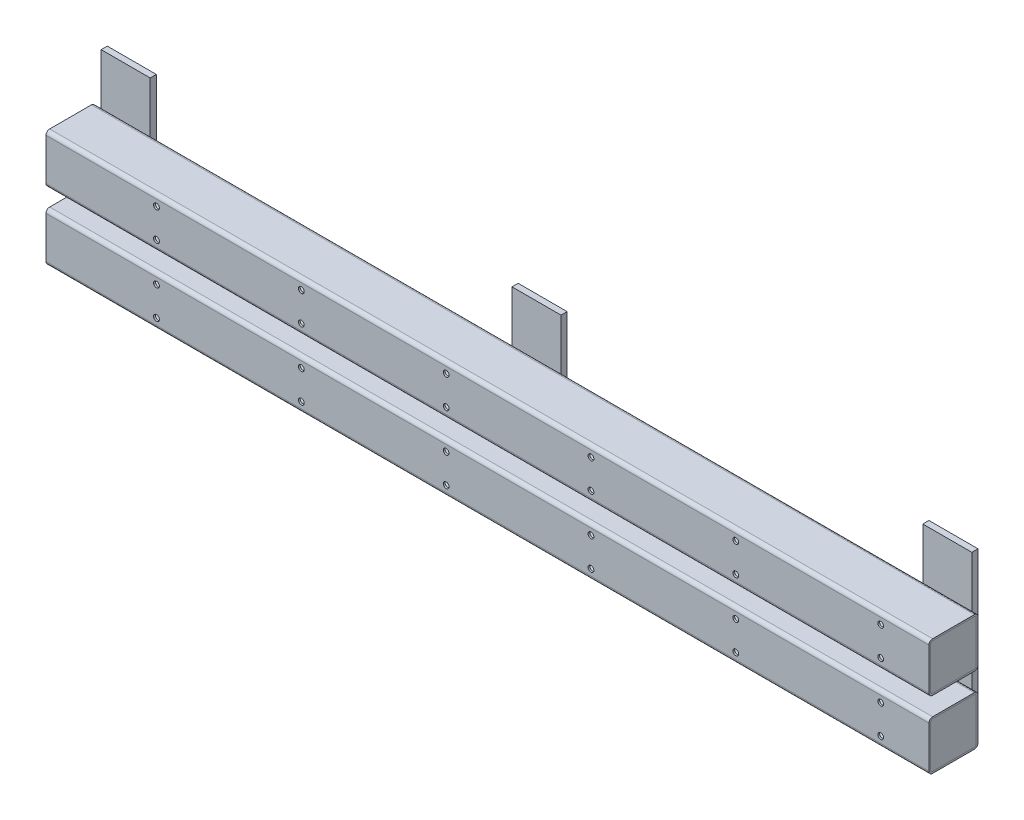
SolidWorks part; units mm, degrees
ref_plane "Front Plane" through (0, 0, 0) normal (0, 0, 1) x (1, 0, 0)
ref_plane "Top Plane" through (0, 0, 0) normal (0, 1, 0) x (1, 0, 0)
ref_plane "Right Plane" through (0, 0, 0) normal (1, 0, 0) x (0, 0, -1)
sketch "Sketch1" plane through (0, 0, 0) normal (0, 0, 1) x (1, 0, 0)
  line L0 (0, 0) -> (914.4, 0)
  line L1 (0, 70) -> (914.4, 70)
  dimension "D1" = 70
  dimension "D2" = 914.4
other "2x2 square tube 2X2X0.725 SQUARE TUBE(1)"
ref_plane "Plane1" through (0, 70, 0) normal (1, 0, 0) x (0, 1, 0)
sketch "Sketch15" plane through (0, 70, 0) normal (1, 0, 0) x (0, 1, 0)
  line L0 (-25.4, 25.4) -> (-21.59, 25.4) construction
  line L1 (-21.59, -25.4) -> (21.59, -25.4)
  line L2 (-25.4, -21.59) -> (-25.4, 21.59)
  line L3 (-21.59, 25.4) -> (21.59, 25.4)
  line L4 (25.4, -21.59) -> (25.4, 21.59)
  line L5 (-24.2841, -24.2841) -> (24.2841, 24.2841) construction
  line L6 (-24.2841, 24.2841) -> (24.2841, -24.2841) construction
  line L7 (-25.4, 25.4) -> (-24.2841, 24.2841) construction
  line L8 (-25.4, 21.59) -> (-25.4, 25.4) construction
  line L9 (-25.4, -25.4) -> (-25.4, -21.59) construction
  line L10 (-25.4, -25.4) -> (-24.2841, -24.2841) construction
  line L11 (-25.4, -25.4) -> (-21.59, -25.4) construction
  line L12 (21.59, -25.4) -> (25.4, -25.4) construction
  line L13 (24.2841, -24.2841) -> (25.4, -25.4) construction
  line L14 (25.4, -25.4) -> (25.4, -21.59) construction
  line L15 (25.4, 21.59) -> (25.4, 25.4) construction
  line L16 (24.2841, 24.2841) -> (25.4, 25.4) construction
  line L17 (21.59, 25.4) -> (25.4, 25.4) construction
  line L18 (23.5585, -21.59) -> (23.5585, 21.59)
  line L19 (-21.59, 23.5585) -> (21.59, 23.5585)
  line L20 (-23.5585, -21.59) -> (-23.5585, 21.59)
  line L21 (-21.59, -23.5585) -> (21.59, -23.5585)
  arc A0 (-25.4, 21.59) -> (-21.59, 25.4) centre (-21.59, 21.59) cw
  arc A1 (-21.59, -25.4) -> (-25.4, -21.59) centre (-21.59, -21.59) cw
  arc A2 (21.59, -25.4) -> (25.4, -21.59) centre (21.59, -21.59) ccw
  arc A3 (25.4, 21.59) -> (21.59, 25.4) centre (21.59, 21.59) ccw
  arc A4 (23.5585, 21.59) -> (21.59, 23.5585) centre (21.59, 21.59) ccw
  arc A5 (-23.5585, 21.59) -> (-21.59, 23.5585) centre (-21.59, 21.59) cw
  arc A6 (-21.59, -23.5585) -> (-23.5585, -21.59) centre (-21.59, -21.59) cw
  arc A7 (21.59, -23.5585) -> (23.5585, -21.59) centre (21.59, -21.59) ccw
  point P0 (0, 0)
  point P34 (0, 0)
  dimension "D2" = 3.81
  dimension "D1" = 50.8
  dimension "D3" = 1.8415
sketch "Sketch12" plane through (0, 0, 0) normal (-1, 0, 0) x (0, 0, 1)
  line L20 (-21.59, -23.5585) -> (21.59, -23.5585)
  line L21 (23.5585, -21.59) -> (23.5585, 21.59)
  line L22 (-23.5585, 21.59) -> (-23.5585, -21.59)
  line L23 (21.59, 23.5585) -> (-21.59, 23.5585)
  line L24 (-21.59, -23.5585) -> (21.59, -23.5585)
  line L25 (23.5585, -21.59) -> (23.5585, 21.59)
  line L26 (-23.5585, 21.59) -> (-23.5585, -21.59)
  line L27 (21.59, 23.5585) -> (-21.59, 23.5585)
  line L48 (-21.59, 46.4415) -> (21.59, 46.4415)
  line L49 (23.5585, 48.41) -> (23.5585, 91.59)
  line L50 (-23.5585, 91.59) -> (-23.5585, 48.41)
  line L51 (21.59, 93.5585) -> (-21.59, 93.5585)
  line L52 (-21.59, 46.4415) -> (21.59, 46.4415)
  line L53 (23.5585, 48.41) -> (23.5585, 91.59)
  line L62 (-23.5585, 91.59) -> (-23.5585, 48.41)
  line L63 (21.59, 93.5585) -> (-21.59, 93.5585)
  arc A18 (-23.5585, -21.59) -> (-21.59, -23.5585) centre (-21.59, -21.59) ccw
  arc A19 (21.59, -23.5585) -> (23.5585, -21.59) centre (21.59, -21.59) ccw
  arc A20 (23.5585, 21.59) -> (21.59, 23.5585) centre (21.59, 21.59) ccw
  arc A21 (-21.59, 23.5585) -> (-23.5585, 21.59) centre (-21.59, 21.59) ccw
  arc A22 (-23.5585, -21.59) -> (-21.59, -23.5585) centre (-21.59, -21.59) ccw
  arc A23 (21.59, -23.5585) -> (23.5585, -21.59) centre (21.59, -21.59) ccw
  arc A24 (23.5585, 21.59) -> (21.59, 23.5585) centre (21.59, 21.59) ccw
  arc A25 (-21.59, 23.5585) -> (-23.5585, 21.59) centre (-21.59, 21.59) ccw
  arc A42 (-23.5585, 48.41) -> (-21.59, 46.4415) centre (-21.59, 48.41) ccw
  arc A43 (21.59, 46.4415) -> (23.5585, 48.41) centre (21.59, 48.41) ccw
  arc A44 (23.5585, 91.59) -> (21.59, 93.5585) centre (21.59, 91.59) ccw
  arc A45 (-21.59, 93.5585) -> (-23.5585, 91.59) centre (-21.59, 91.59) ccw
  arc A46 (-23.5585, 48.41) -> (-21.59, 46.4415) centre (-21.59, 48.41) ccw
  arc A55 (21.59, 46.4415) -> (23.5585, 48.41) centre (21.59, 48.41) ccw
  arc A56 (23.5585, 91.59) -> (21.59, 93.5585) centre (21.59, 91.59) ccw
  arc A57 (-21.59, 93.5585) -> (-23.5585, 91.59) centre (-21.59, 91.59) ccw
  dimension "D1" = 0
  dimension "D2" = 0
extrude "Boss-Extrude1" add sketch "Sketch12" against normal blind 3 separate body
sketch "Sketch17" plane through (914.4, 0, 0) normal (1, 0, 0) x (0, 0, -1)
  line L8 (23.5585, -21.59) -> (23.5585, 21.59)
  line L9 (21.59, 23.5585) -> (-21.59, 23.5585)
  line L10 (-23.5585, 21.59) -> (-23.5585, -21.59)
  line L11 (-21.59, -23.5585) -> (21.59, -23.5585)
  line L12 (23.5585, -21.59) -> (23.5585, 21.59)
  line L13 (21.59, 23.5585) -> (-21.59, 23.5585)
  line L14 (-23.5585, 21.59) -> (-23.5585, -21.59)
  line L15 (-21.59, -23.5585) -> (21.59, -23.5585)
  line L20 (23.5585, 48.41) -> (23.5585, 91.59)
  line L21 (21.59, 93.5585) -> (-21.59, 93.5585)
  line L22 (-23.5585, 91.59) -> (-23.5585, 48.41)
  line L23 (-21.59, 46.4415) -> (21.59, 46.4415)
  line L24 (23.5585, 48.41) -> (23.5585, 91.59)
  line L25 (21.59, 93.5585) -> (-21.59, 93.5585)
  line L26 (-23.5585, 91.59) -> (-23.5585, 48.41)
  line L27 (-21.59, 46.4415) -> (21.59, 46.4415)
  arc A8 (21.59, -23.5585) -> (23.5585, -21.59) centre (21.59, -21.59) ccw
  arc A9 (23.5585, 21.59) -> (21.59, 23.5585) centre (21.59, 21.59) ccw
  arc A10 (-21.59, 23.5585) -> (-23.5585, 21.59) centre (-21.59, 21.59) ccw
  arc A11 (-23.5585, -21.59) -> (-21.59, -23.5585) centre (-21.59, -21.59) ccw
  arc A12 (21.59, -23.5585) -> (23.5585, -21.59) centre (21.59, -21.59) ccw
  arc A13 (23.5585, 21.59) -> (21.59, 23.5585) centre (21.59, 21.59) ccw
  arc A14 (-21.59, 23.5585) -> (-23.5585, 21.59) centre (-21.59, 21.59) ccw
  arc A15 (-23.5585, -21.59) -> (-21.59, -23.5585) centre (-21.59, -21.59) ccw
  arc A20 (21.59, 46.4415) -> (23.5585, 48.41) centre (21.59, 48.41) ccw
  arc A21 (23.5585, 91.59) -> (21.59, 93.5585) centre (21.59, 91.59) ccw
  arc A22 (-21.59, 93.5585) -> (-23.5585, 91.59) centre (-21.59, 91.59) ccw
  arc A23 (-23.5585, 48.41) -> (-21.59, 46.4415) centre (-21.59, 48.41) ccw
  arc A24 (21.59, 46.4415) -> (23.5585, 48.41) centre (21.59, 48.41) ccw
  arc A25 (23.5585, 91.59) -> (21.59, 93.5585) centre (21.59, 91.59) ccw
  arc A26 (-21.59, 93.5585) -> (-23.5585, 91.59) centre (-21.59, 91.59) ccw
  arc A27 (-23.5585, 48.41) -> (-21.59, 46.4415) centre (-21.59, 48.41) ccw
  dimension "D1" = 0
  dimension "D2" = 0
extrude "Boss-Extrude4" add sketch "Sketch17" against normal blind 6.35 separate body
sketch "Sketch13" plane through (0, 0, -25.4) normal (0, 0, -1) x (-1, 0, 0)
  line L0 (-914.4, 44.6) -> (-914.4, 25.4) construction
  line L9 (0, 44.6) -> (0, 25.4) construction
  line L11 (-6.35, 35) -> (-57.15, 35) construction
  line L12 (-57.15, 35) -> (-857.25, 35) construction
  line L13 (-857.25, 35) -> (-908.05, 35) construction
  line L14 (-908.05, 35) -> (-914.4, 35) construction
  line L16 (-908.05, -76.2) -> (-857.25, -76.2) construction
  line L17 (-908.05, -25.4) -> (-908.05, 146.2)
  line L18 (-908.05, 146.2) -> (-857.25, 146.2)
  line L19 (-857.25, -25.4) -> (-857.25, 146.2)
  line L20 (-896.4464, -25.4) -> (-857.25, 146.2) construction
  line L21 (-908.05, 146.2) -> (-868.8536, -25.4) construction
  line L22 (-482.6, -76.2) -> (-431.8, -76.2) construction
  line L23 (-482.6, -25.4) -> (-482.6, 146.2)
  line L24 (-482.6, 146.2) -> (-431.8, 146.2)
  line L25 (-431.8, -25.4) -> (-431.8, 146.2)
  line L26 (-470.9964, -25.4) -> (-431.8, 146.2) construction
  line L27 (-482.6, 146.2) -> (-443.4036, -25.4) construction
  line L28 (-57.15, -76.2) -> (-6.35, -76.2) construction
  line L29 (-57.15, -25.4) -> (-57.15, 146.2)
  line L30 (-57.15, 146.2) -> (-6.35, 146.2)
  line L31 (-6.35, -25.4) -> (-6.35, 146.2)
  line L32 (-45.5464, -25.4) -> (-6.35, 146.2) construction
  line L33 (-57.15, 146.2) -> (-17.9536, -25.4) construction
  line L35 (-482.6, -25.4) -> (-431.8, -25.4)
  line L36 (-57.15, -25.4) -> (-6.35, -25.4)
  line L37 (-57.15, -76.2) -> (-57.15, -25.4) construction
  line L38 (-57.15, -76.2) -> (-45.5464, -25.4) construction
  line L39 (-6.35, -76.2) -> (-6.35, -25.4) construction
  line L40 (-17.9536, -25.4) -> (-6.35, -76.2) construction
  line L41 (-431.8, -76.2) -> (-431.8, -25.4) construction
  line L42 (-443.4036, -25.4) -> (-431.8, -76.2) construction
  line L43 (-482.6, -76.2) -> (-470.9964, -25.4) construction
  line L44 (-482.6, -76.2) -> (-482.6, -25.4) construction
  line L45 (-857.25, -76.2) -> (-857.25, -25.4) construction
  line L46 (-868.8536, -25.4) -> (-857.25, -76.2) construction
  line L47 (-908.05, -76.2) -> (-896.4464, -25.4) construction
  line L48 (-908.05, -76.2) -> (-908.05, -25.4) construction
  line L49 (-908.05, -25.4) -> (-857.25, -25.4)
  line L50 (0, 35) -> (-6.35, 35) construction
  point P8 (-882.65, 35)
  point P15 (-457.2, 35)
  point P20 (-31.75, 35)
  dimension "D2" = 50.8
  dimension "D3" = 50.8
  dimension "D4" = 222.4
extrude "Boss-Extrude3" add sketch "Sketch13" along normal blind 6.35 separate body
sketch "Sketch16" plane through (0, 0, 25.4) normal (0, 0, 1) x (1, 0, 0)
  line L0 (864.4, 693.7059) -> (864.4, -650.7882) construction
  line L1 (914.4, 91.59) -> (914.4, 48.41) construction
  line L2 (914.4, 44.6) -> (914.4, 25.4) construction
  line L3 (707.6546, 35) -> (1121.1454, 35) construction
  circle A0 centre (864.4, 85) radius 3
  circle A1 centre (864.4, 55) radius 3
  circle A2 centre (864.4, 15) radius 3
  circle A3 centre (864.4, -15) radius 3
  point P19 (914.4, 35)
  dimension "D2" = 6
  dimension "D1" = 50
  dimension "D3" = 30
  dimension "D4" = 30
  dimension "D5" = 70
  dimension "D6" = 20
extrude "Cut-Extrude1" cut sketch "Sketch16" against normal up to next (1.8415 mm away)
pattern_linear "LPattern1" count 6 spacing 150 along (-1, 0, 0) of "Cut-Extrude1"
sketch "Sketch18" plane through (0, 0, 0) normal (-1, 0, 0) x (0, 0, 1)
  line L0 (-12.7, 147.7427) -> (-12.7, -72.0368) construction
  line L1 (-25.4, -25.4) -> (-25.4, 146.2) construction
  line L2 (-21.59, 95.4) -> (21.59, 95.4) construction
  line L4 (21.59, -25.4) -> (-21.59, -25.4) construction
  circle A0 centre (-12.7, -12.7) radius 3
  circle A1 centre (-12.7, 12.7) radius 3
  circle A2 centre (-12.7, 57.3) radius 3
  circle A3 centre (-12.7, 82.7) radius 3
  dimension "D6" = 6
  dimension "D1" = 12.7
  dimension "D2" = 12.7
  dimension "D3" = 25.4
  dimension "D4" = 12.7
  dimension "D5" = 25.4
extrude "Cut-Extrude2" cut sketch "Sketch18" against normal up to next (3 mm away)
